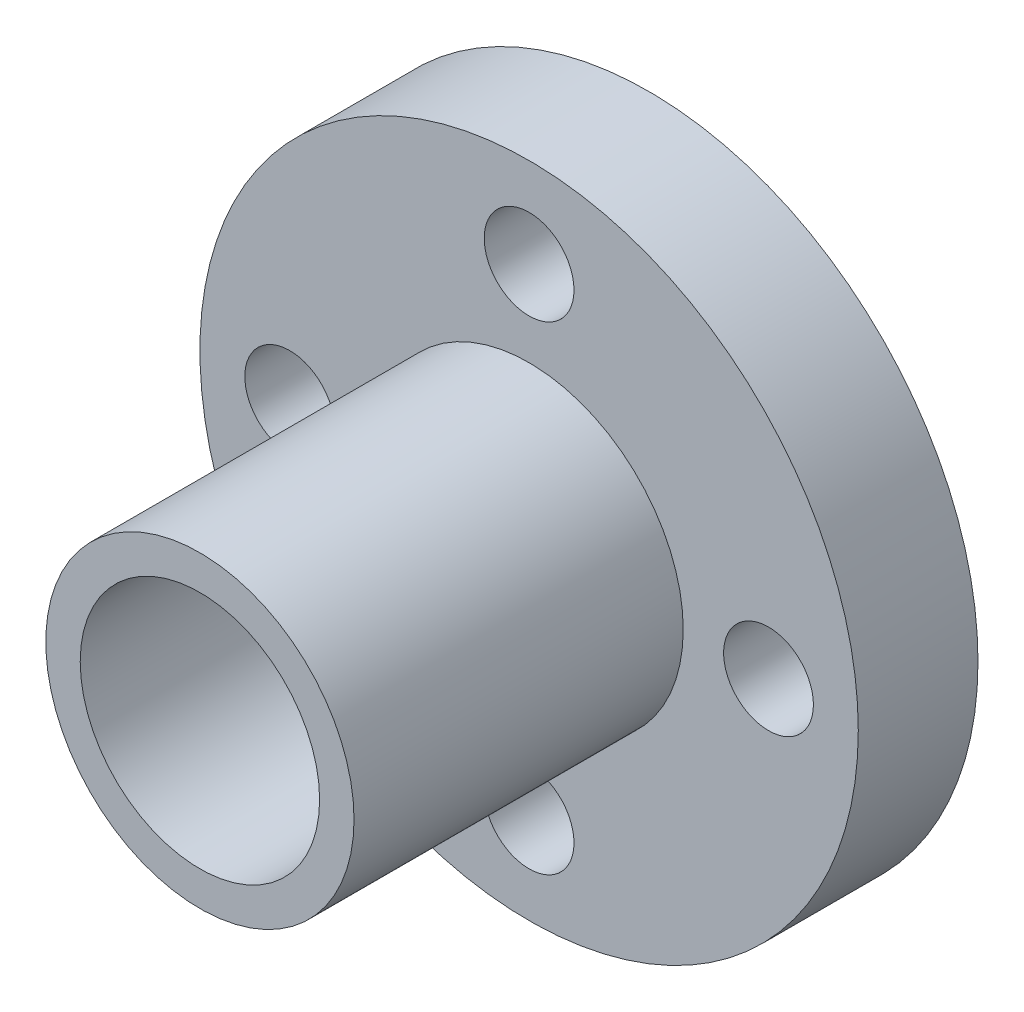
SolidWorks part; units mm, degrees
ref_plane "Front Plane" through (0, 0, 0) normal (0, 0, 1) x (1, 0, 0)
ref_plane "Top Plane" through (0, 0, 0) normal (0, 1, 0) x (1, 0, 0)
ref_plane "Right Plane" through (0, 0, 0) normal (1, 0, 0) x (0, 0, -1)
sketch "Sketch1" plane through (0, 0, 0) normal (0, 0, 1) x (1, 0, 0)
  circle A0 centre (0, 0) radius 11
  dimension "D1" = 22
extrude "Boss-Extrude1" add sketch "Sketch1" along normal blind 4
sketch "Sketch2" plane through (0, 0, 4) normal (0, 0, 1) x (1, 0, 0)
  circle A0 centre (0, 0) radius 5.15
  dimension "D1" = 10.3
extrude "Boss-Extrude2" add sketch "Sketch2" along normal blind 11
sketch "Sketch3" plane through (0, 0, 15) normal (0, 0, 1) x (1, 0, 0)
  circle A0 centre (0, 0) radius 4
  dimension "D1" = 8
extrude "Cut-Extrude1" cut sketch "Sketch3" against normal through all
sketch "Sketch4" plane through (0, 0, 4) normal (0, 0, 1) x (1, 0, 0)
  line L0 (0, 11) -> (0, 0) construction
  line L1 (0, 0) -> (-11, 0) construction
  circle A0 centre (0, 0) radius 11 construction
  circle A1 centre (0, 8) radius 1.5
  circle A2 centre (8, 0) radius 1.5
  circle A3 centre (0, -8) radius 1.5
  circle A4 centre (-8, 0) radius 1.5
  point P13 (0, 0)
  dimension "D1" = 3
  dimension "D2" = 8
  dimension "D3" = 4
extrude "Cut-Extrude2" cut sketch "Sketch4" against normal through all
